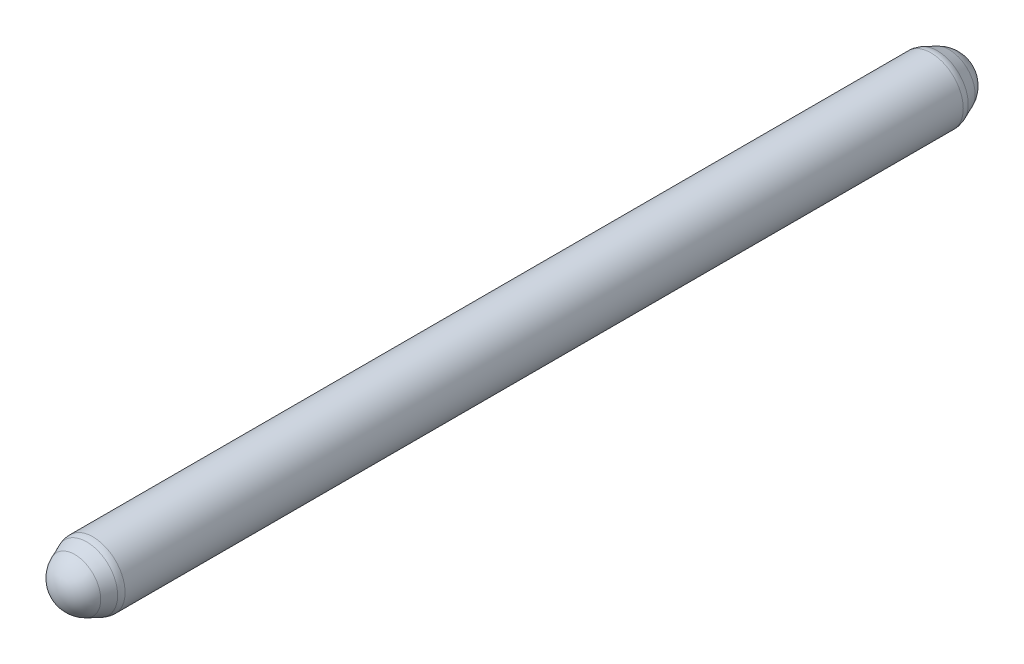
SolidWorks part; units mm, degrees
ref_plane "Front Plane" through (0, 0, 0) normal (0, 0, 1) x (1, 0, 0)
ref_plane "Top Plane" through (0, 0, 0) normal (0, 1, 0) x (1, 0, 0)
ref_plane "Right Plane" through (0, 0, 0) normal (1, 0, 0) x (0, 0, -1)
sketch "Sketch1" plane through (0, 0, 0) normal (0, 0, 1) x (1, 0, 0)
  circle A0 centre (0, 0) radius 20
  dimension "D1" = 40
extrude "Boss-Extrude1" add sketch "Sketch1" along normal mid plane 525
sketch "Sketch2" plane through (0, 0, 0) normal (1, 0, 0) x (0, 0, -1)
  line L0 (-262.5, 20) -> (-262.5, 0)
  line L1 (-262.5, 20) -> (-262.5, -20) construction
  line L2 (-262.5, 0) -> (-282.5, 0)
  line L3 (-262.5, 20) -> (-271.7637, 16.1264)
  arc A0 (-271.7637, 16.1264) -> (-282.5, 0) centre (-265.0205, 0) ccw
  dimension "D1" = 20
  dimension "D3" = 0
revolve "Revolve1" add sketch "Sketch2" angle 360 about L2
mirror "Mirror1" about plane through (0, 0, 0) normal (0, 0, 1) of "Revolve1"
fillet "Fillet1" radius 10 2 edges at (20, 0, 262.5) (0, 20, -262.5)
